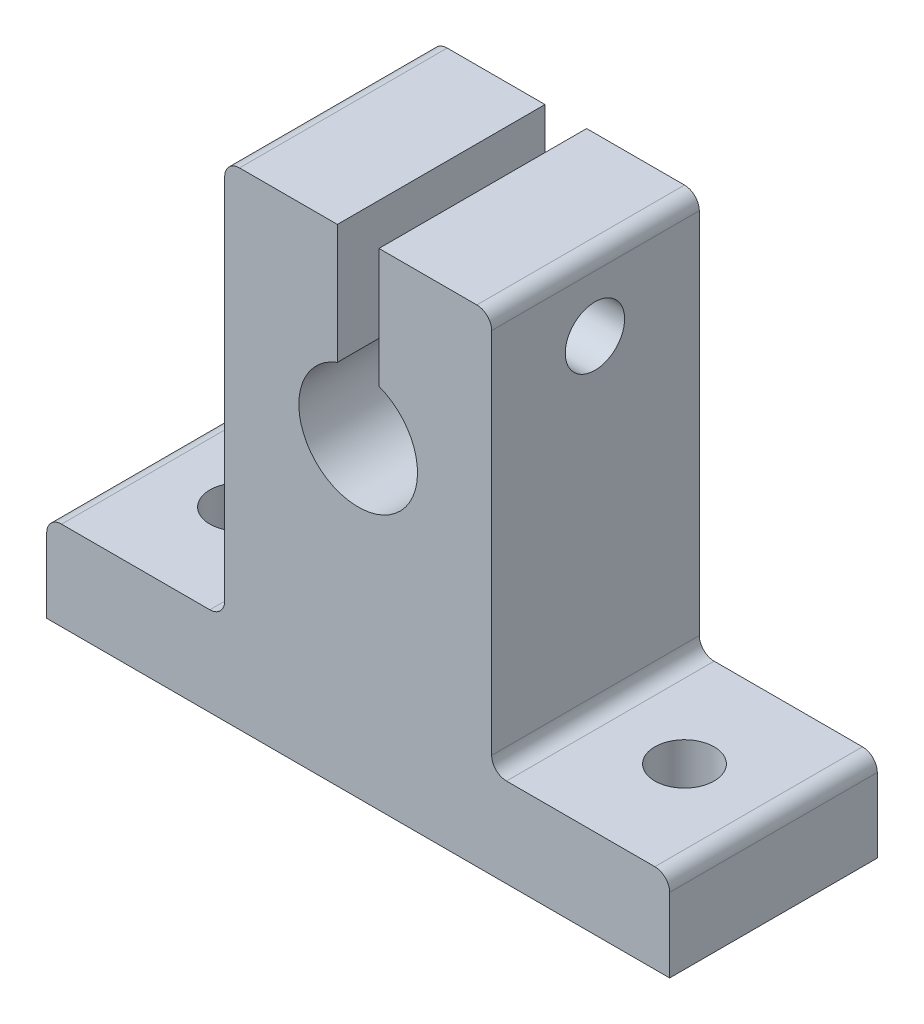
SolidWorks part; units mm, degrees
ref_plane "Ön Düzlem" through (0, 0, 0) normal (0, 0, 1) x (1, 0, 0)
ref_plane "Üst Düzlem" through (0, 0, 0) normal (0, 1, 0) x (1, 0, 0)
ref_plane "Sağ Düzlem" through (0, 0, 0) normal (1, 0, 0) x (0, 0, -1)
sketch "Çizim1" plane through (0, 0, 0) normal (0, 0, 1) x (1, 0, 0)
  line L0 (-58.3707, 0) -> (-16.3707, 0)
  line L1 (-16.3707, 0) -> (-16.3707, 5)
  line L2 (-17.3707, 6) -> (-27.3707, 6)
  line L3 (-28.3707, 7) -> (-28.3707, 31.8)
  line L4 (-45.3707, 32.8) -> (-38.7732, 32.8)
  line L5 (-35.9681, 32.8) -> (-35.9681, 24.746)
  line L6 (-46.3707, 7) -> (-46.3707, 31.8)
  line L7 (-57.3707, 6) -> (-47.3707, 6)
  line L8 (-58.3707, 0) -> (-58.3707, 5)
  line L9 (-29.3707, 32.8) -> (-35.9681, 32.8)
  line L11 (-38.7732, 32.8) -> (-38.7732, 24.746)
  arc A0 (-38.7732, 24.746) -> (-35.9681, 24.746) centre (-37.3707, 21) ccw
  arc A1 (-28.3707, 7) -> (-27.3707, 6) centre (-27.3707, 7) ccw
  arc A2 (-16.3707, 5) -> (-17.3707, 6) centre (-17.3707, 5) ccw
  arc A3 (-58.3707, 5) -> (-57.3707, 6) centre (-57.3707, 5) cw
  arc A4 (-47.3707, 6) -> (-46.3707, 7) centre (-47.3707, 7) ccw
  arc A5 (-28.3707, 31.8) -> (-29.3707, 32.8) centre (-29.3707, 31.8) ccw
  arc A6 (-46.3707, 31.8) -> (-45.3707, 32.8) centre (-45.3707, 31.8) cw
  dimension "D1" = 1
extrude "Yükseklik-Ekstrüzyon1" add sketch "Çizim1" along normal blind 14
sketch "Çizim2" plane through (0, 6, 0) normal (0, 1, 0) x (1, 0, 0)
  circle A0 centre (-22.3707, -7) radius 2
  circle A1 centre (-52.3707, -7) radius 2
extrude "Kes-Ekstrüzyon1" cut sketch "Çizim2" against normal blind 14
sketch "Çizim3" plane through (-28.3707, 0, 0) normal (1, 0, 0) x (0, 0, -1)
  circle A0 centre (-7.0375, 28) radius 2
extrude "Kes-Ekstrüzyon2" cut sketch "Çizim3" against normal blind 50
